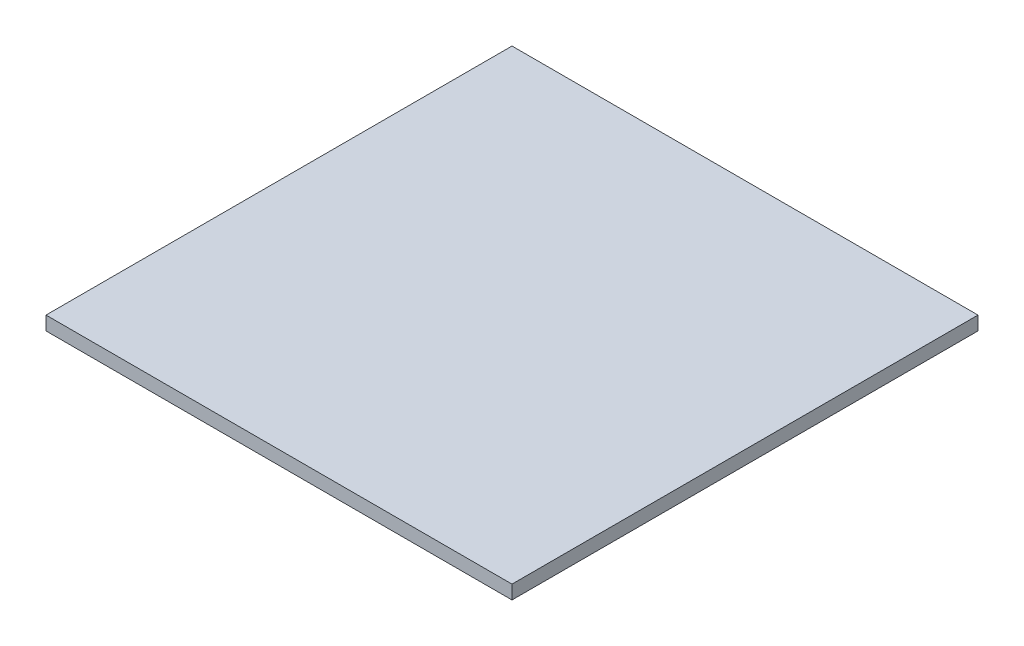
SolidWorks part; units mm, degrees
ref_plane "前视基准面" through (0, 0, 0) normal (0, 0, 1) x (1, 0, 0)
ref_plane "上视基准面" through (0, 0, 0) normal (0, 1, 0) x (1, 0, 0)
ref_plane "右视基准面" through (0, 0, 0) normal (1, 0, 0) x (0, 0, -1)
sketch "草图1" plane through (0, 0, 0) normal (0, 1, 0) x (1, 0, 0)
  line L1 (-25.4, -25.4) -> (25.4, -25.4)
  line L2 (-25.4, -25.4) -> (-25.4, 25.4)
  line L3 (-25.4, 25.4) -> (25.4, 25.4)
  line L4 (25.4, -25.4) -> (25.4, 25.4)
  line L5 (-25.4, -25.4) -> (25.4, 25.4) construction
  line L6 (-25.4, 25.4) -> (25.4, -25.4) construction
  point P0 (0, 0)
  dimension "D1" = 50.8
  dimension "D2" = 50.8
extrude "凸台-拉伸1" add sketch "草图1" along normal blind 1.5
